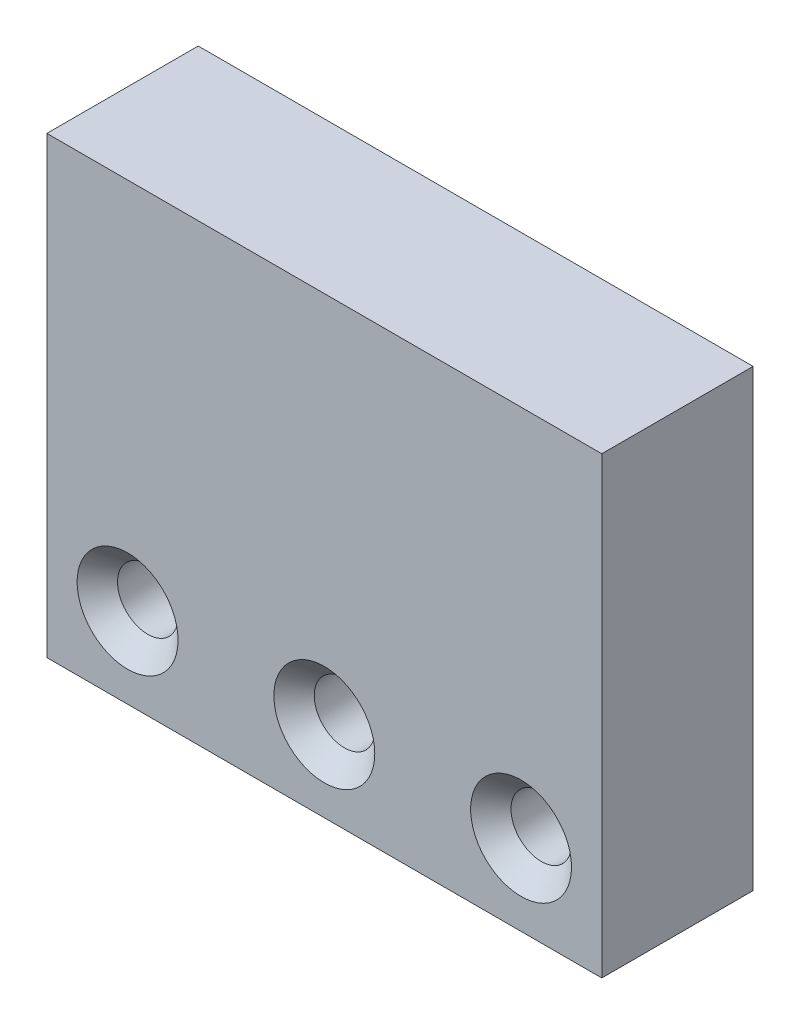
SolidWorks part; units mm, degrees
material "Plain Carbon Steel"
ref_plane "Front Plane" through (0, 0, 0) normal (0, 0, 1) x (1, 0, 0)
ref_plane "Top Plane" through (0, 0, 0) normal (0, 1, 0) x (1, 0, 0)
ref_plane "Right Plane" through (0, 0, 0) normal (1, 0, 0) x (0, 0, -1)
sketch "Sketch1" plane through (0, 0, 0) normal (0, 0, 1) x (1, 0, 0)
  line L1 (0, 0) -> (55, 0)
  line L2 (0, 0) -> (0, 45)
  line L3 (0, 45) -> (55, 45)
  line L4 (55, 0) -> (55, 45)
  dimension "D1" = 55
  dimension "D2" = 45
extrude "Boss-Extrude1" add sketch "Sketch1" along normal mid plane 15
hole_wizard "Ø6.0mm Dowel Hole1" positions "3DSketch1" profile "Sketch2" hole size "Ø6.0" standard "ANSI Metric" end condition through all
sketch3d "3DSketch1"
  line L0 (0, 0, 7.5) -> (55, 0, 7.5) construction
  point P0 (8, 8, 7.5)
  point P2 (27.5, 8, 7.5)
  point P4 (47, 8, 7.5)
  dimension "D1" = 8
sketch "Sketch2" plane through (8, 8, 7.5) normal (1, 0, 0) x (0, -1, 0)
  line L0 (0, 0) -> (0, 15)
  line L1 (0, 15) -> (3, 15)
  line L2 (3, 15) -> (3, 2)
  line L3 (3, 2) -> (5, 0)
  line L5 (5, 0) -> (0, 0)
  line L6 (-3, 2) -> (-5, 0) construction
  line L11 (0, -6.35) -> (0, 107.95) construction
  dimension "Thru Hole Dia." = 6
  dimension "Thru Hole Depth" = 15
  dimension "Near C'Sink Dia." = 10
  dimension "Near C'Sink Angle" = 90
hole_wizard "Tap Drill for M5x0.8 Tap2" positions "3DSketch3" profile "Sketch4" hole size "M5x0.8" standard "ANSI Metric"
sketch3d "3DSketch3"
  point P0 (45, 36, -7.5)
  point P2 (10, 36, -7.5)
sketch "Sketch4" plane through (45, 36, -7.5) normal (1, 0, 0) x (0, 1, 0)
  line L0 (0, 0) -> (0, 11.2618)
  line L1 (0, 11.2618) -> (2.1, 10)
  line L2 (2.1, 10) -> (2.1, 0)
  line L5 (2.1, 0) -> (0, 0)
  line L10 (0, 11.2618) -> (-2.1, 10) construction
  line L11 (0, -6.35) -> (0, 107.95) construction
  dimension "Hole Dia." = 4.2
  dimension "Hole Depth" = 10
  dimension "Drill Angle" = 118
